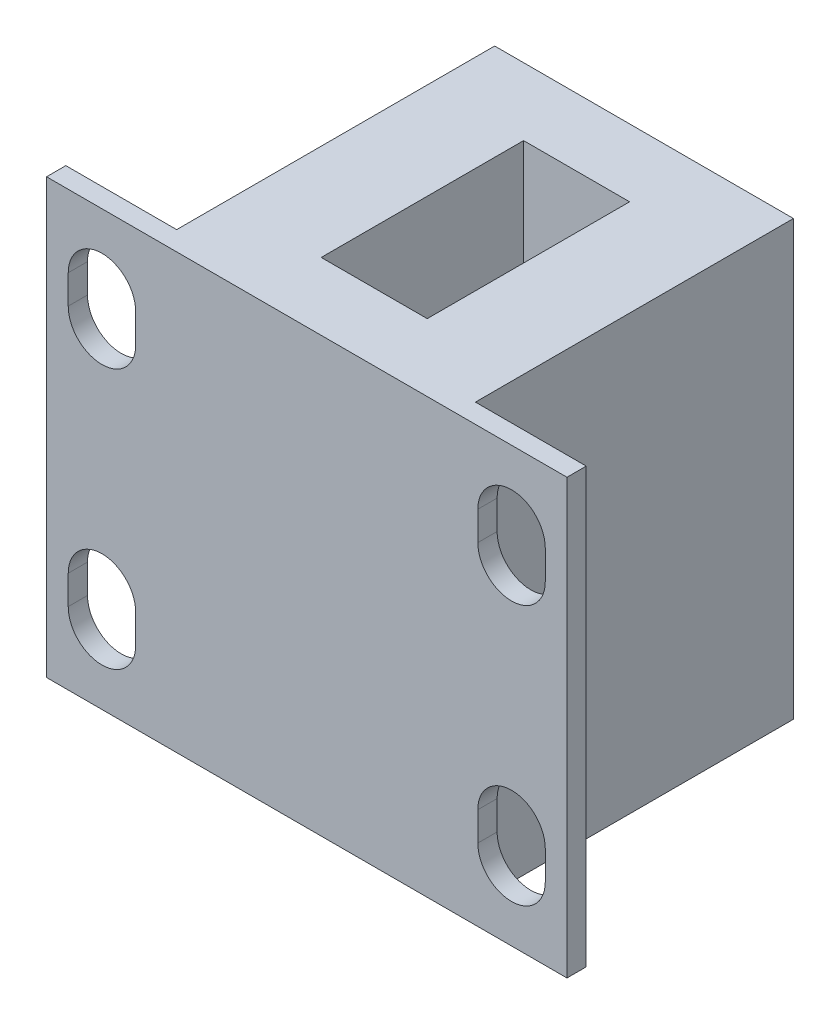
SolidWorks part; units mm, degrees
ref_plane "Front Plane" through (0, 0, 0) normal (0, 0, 1) x (1, 0, 0)
ref_plane "Top Plane" through (0, 0, 0) normal (0, 1, 0) x (1, 0, 0)
ref_plane "Right Plane" through (0, 0, 0) normal (1, 0, 0) x (0, 0, -1)
sketch "Sketch1" plane through (0, 0, 0) normal (0, 1, 0) x (1, 0, 0)
  line L0 (7.75, -7.75) -> (13.5, -7.75)
  line L1 (-7.75, 8.75) -> (7.75, 8.75)
  line L2 (-7.75, 8.75) -> (-7.75, -8.75)
  line L3 (-7.75, -8.75) -> (7.75, -8.75)
  line L4 (7.75, 8.75) -> (7.75, -8.75)
  line L5 (-7.75, 8.75) -> (7.75, -8.75) construction
  line L6 (-7.75, -8.75) -> (7.75, 8.75) construction
  line L7 (13.5, -7.75) -> (13.5, -8.75)
  line L8 (13.5, -8.75) -> (7.75, -8.75)
  line L9 (-7.75, -8.75) -> (-13.5, -8.75)
  line L10 (-13.5, -8.75) -> (-13.5, -7.75)
  line L11 (-13.5, -7.75) -> (-7.75, -7.75)
  point P0 (0, 0)
  dimension "D1" = 27
  dimension "D2" = 15.5
  dimension "D3" = 17.5
  dimension "D4" = 1
extrude "Boss-Extrude1" add sketch "Sketch1" along normal blind 22.5 contours L4 L1 L2 L3 | L8 L7 L0 L4 | L11 L10 L9 L2
sketch "Sketch2" plane through (0, 0, 7.75) normal (0, 0, -1) x (-1, 0, 0)
  line L0 (10.625, 18.75) -> (10.625, 17.25) construction
  line L1 (12.375, 18.75) -> (12.375, 17.25)
  line L2 (8.875, 18.75) -> (8.875, 17.25)
  line L3 (13.5, 22.5) -> (7.75, 22.5) construction
  arc A0 (12.375, 18.75) -> (8.875, 18.75) centre (10.625, 18.75) ccw
  arc A1 (8.875, 17.25) -> (12.375, 17.25) centre (10.625, 17.25) ccw
  point P2 (10.625, 18)
  point P9 (10.625, 22.5)
  point P10 (10.625, 20.5)
  point P11 (10.625, 15.5)
  point P14 (10.8546, 21.067)
  dimension "D1" = 3.5
  dimension "D2" = 5
  dimension "D3" = 2
extrude "Cut-Extrude1" cut sketch "Sketch2" against normal through all
mirror "Mirror1" about plane through (0, 0, 0) normal (1, 0, 0) of "Cut-Extrude1"
ref_plane "Plane1" through (0, 11.25, 0) normal (0, 1, 0) x (1, 0, 0)
mirror "Mirror2" about plane through (0, 11.25, 0) normal (0, 1, 0) of "Mirror1", "Cut-Extrude1"
sketch "Sketch3" plane through (0, 22.5, 0) normal (0, 1, 0) x (1, 0, 0)
  line L1 (2.75, -5.25) -> (-2.75, -5.25)
  line L2 (2.75, -5.25) -> (2.75, 5.25)
  line L3 (2.75, 5.25) -> (-2.75, 5.25)
  line L4 (-2.75, -5.25) -> (-2.75, 5.25)
  line L5 (2.75, -5.25) -> (-2.75, 5.25) construction
  line L6 (2.75, 5.25) -> (-2.75, -5.25) construction
  point P0 (0, 0)
  dimension "D1" = 10.5
  dimension "D2" = 5.5
extrude "Cut-Extrude2" cut sketch "Sketch3" against normal blind 10
